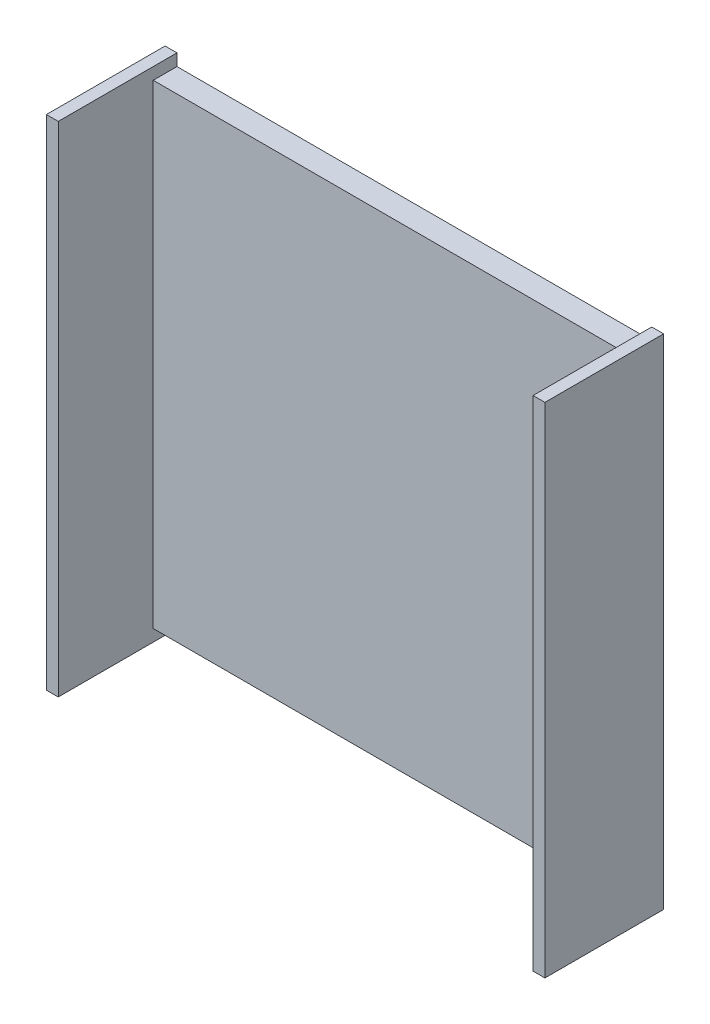
SolidWorks part; units mm, degrees
ref_plane "Front Plane" through (0, 0, 0) normal (0, 0, 1) x (1, 0, 0)
ref_plane "Top Plane" through (0, 0, 0) normal (0, 1, 0) x (1, 0, 0)
ref_plane "Right Plane" through (0, 0, 0) normal (1, 0, 0) x (0, 0, -1)
sketch "Sketch1" plane through (0, 0, 0) normal (0, 0, 1) x (1, 0, 0)
  line L1 (-21, 21) -> (21, 21)
  line L2 (-21, 21) -> (-21, -21)
  line L3 (-21, -21) -> (21, -21)
  line L4 (21, 21) -> (21, -21)
  line L5 (-21, 21) -> (21, -21) construction
  line L6 (-21, -21) -> (21, 21) construction
  line L7 (-20, -20) -> (20, -20)
  line L8 (-20, -20) -> (-20, 20)
  line L9 (-20, 20) -> (20, 20)
  line L10 (20, -20) -> (20, 20)
  line L11 (-20, -20) -> (20, 20) construction
  line L12 (-20, 20) -> (20, -20) construction
  point P0 (0, 0)
  point P6 (0, 0)
  dimension "D1" = 42
  dimension "D2" = 42
  dimension "D3" = 40
  dimension "D4" = 40
extrude "Boss-Extrude1" add sketch "Sketch1" along normal blind 10
sketch "Sketch3" plane through (-20, 0, 0) normal (1, 0, 0) x (0, 0, -1)
  line L0 (-10, -20) -> (0, -20) construction
  line L1 (0, 20) -> (-2, 20)
  line L2 (0, 20) -> (0, -20)
  line L3 (0, -20) -> (-2, -20)
  line L4 (-2, 20) -> (-2, -20)
  dimension "D1" = 2
extrude "Boss-Extrude2" add sketch "Sketch3" along normal blind 40
sketch "Sketch5" plane through (0, 0, 10) normal (0, 0, 1) x (1, 0, 0)
  line L0 (21, 21) -> (-21, 21) construction
  line L1 (-20, 20) -> (20, 20)
  line L2 (-20, 20) -> (-20, 21)
  line L3 (-20, 21) -> (20, 21)
  line L4 (20, 20) -> (20, 21)
  dimension "D1" = 40
extrude "Cut-Extrude1" cut sketch "Sketch5" against normal blind 10
sketch "Sketch6" plane through (0, 0, 10) normal (0, 0, 1) x (1, 0, 0)
  line L0 (-21, -21) -> (21, -21) construction
  line L1 (20, -20) -> (-20, -20)
  line L2 (20, -20) -> (20, -21)
  line L3 (20, -21) -> (-20, -21)
  line L4 (-20, -20) -> (-20, -21)
  dimension "D1" = 40
extrude "Cut-Extrude2" cut sketch "Sketch6" against normal blind 10
